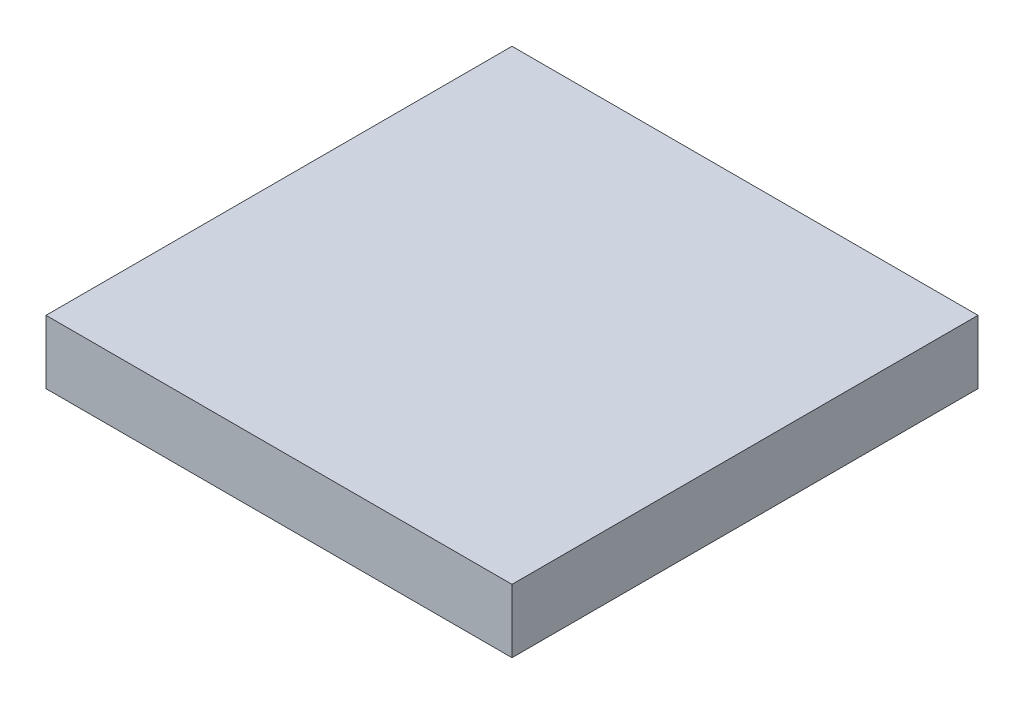
SolidWorks part; units mm, degrees
ref_plane "Front" through (0, 0, 0) normal (0, 0, 1) x (1, 0, 0)
ref_plane "Top" through (0, 0, 0) normal (0, 1, 0) x (1, 0, 0)
ref_plane "Right" through (0, 0, 0) normal (1, 0, 0) x (0, 0, -1)
sketch "Sketch1" plane through (0, 0, 0) normal (0, 1, 0) x (1, 0, 0)
  line L1 (0, 0) -> (22, 0)
  line L2 (0, 0) -> (0, 22)
  line L3 (0, 22) -> (22, 22)
  line L4 (22, 0) -> (22, 22)
  dimension "D1" = 22
extrude "Boss-Extrude1" add sketch "Sketch1" along normal blind 3
